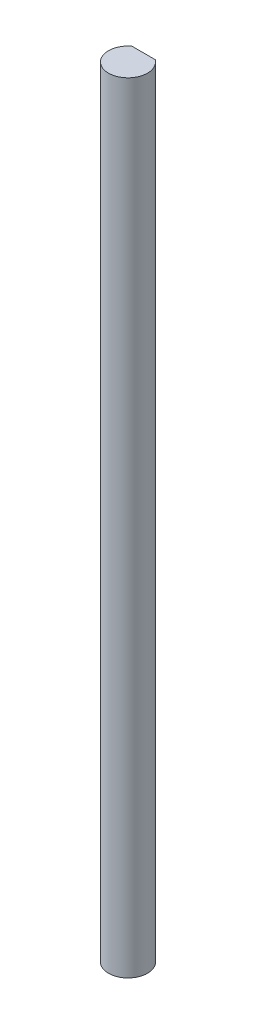
SolidWorks part; units mm, degrees
ref_plane "Front Plane" through (0, 0, 0) normal (0, 0, 1) x (1, 0, 0)
ref_plane "Top Plane" through (0, 0, 0) normal (0, 1, 0) x (1, 0, 0)
ref_plane "Right Plane" through (0, 0, 0) normal (1, 0, 0) x (0, 0, -1)
sketch "Sketch1" plane through (0, 0, 0) normal (0, 1, 0) x (1, 0, 0)
  line L0 (-1.905, 2.54) -> (1.905, 2.54)
  arc A0 (-1.905, 2.54) -> (1.905, 2.54) centre (0, 0) ccw
  dimension "D1" = 6.35
  dimension "D2" = 2.54
extrude "Boss-Extrude1" add sketch "Sketch1" along normal blind 127
